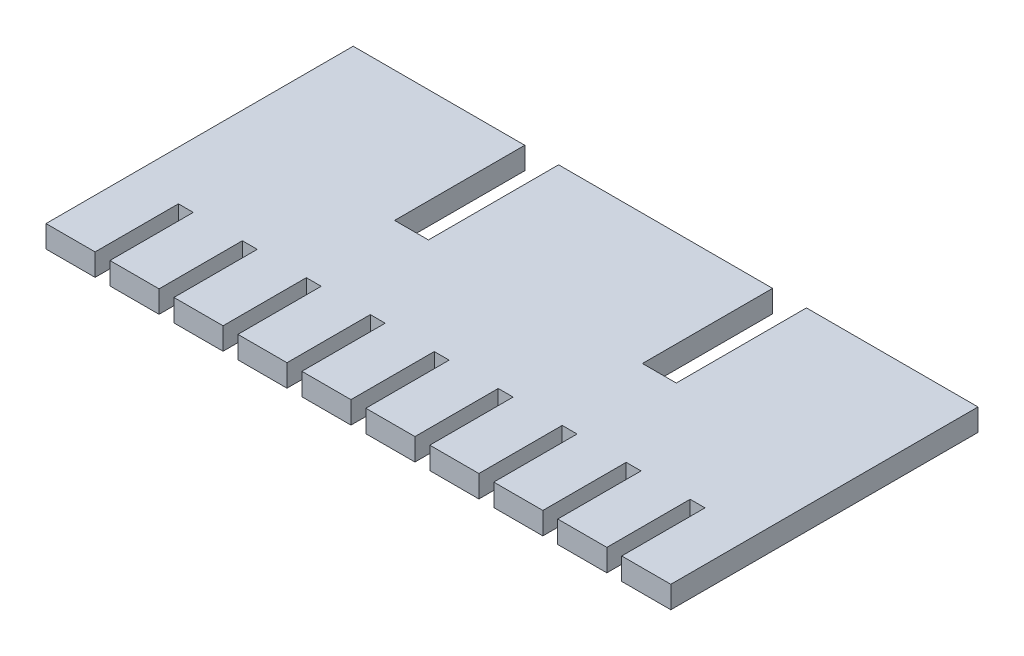
SolidWorks part; units mm, degrees
ref_plane "Front Plane" through (0, 0, 0) normal (0, 0, 1) x (1, 0, 0)
ref_plane "Top Plane" through (0, 0, 0) normal (0, 1, 0) x (1, 0, 0)
ref_plane "Right Plane" through (0, 0, 0) normal (1, 0, 0) x (0, 0, -1)
sketch "Sketch1" plane through (0, 0, 0) normal (0, 1, 0) x (1, 0, 0)
  line L0 (0, 0) -> (0, -29.5)
  line L1 (0, -29.5) -> (4.7139, -29.5)
  line L2 (4.7139, -29.5) -> (4.7139, -21.5)
  line L3 (4.7139, -21.5) -> (6.1429, -21.5)
  line L4 (6.1429, -21.5) -> (6.1429, -29.5)
  line L5 (6.1429, -29.5) -> (10.8568, -29.5)
  line L6 (10.8568, -29.5) -> (10.8568, -21.5)
  line L7 (10.8568, -21.5) -> (12.2858, -21.5)
  line L8 (12.2858, -21.5) -> (12.2858, -29.5)
  line L9 (12.2858, -29.5) -> (16.9997, -29.5)
  line L10 (16.9997, -29.5) -> (16.9997, -21.5)
  line L11 (16.9997, -21.5) -> (18.4287, -21.5)
  line L12 (18.4287, -21.5) -> (18.4287, -29.5)
  line L13 (18.4287, -29.5) -> (23.1426, -29.5)
  line L14 (23.1426, -29.5) -> (23.1426, -21.5)
  line L15 (23.1426, -21.5) -> (24.5716, -21.5)
  line L16 (24.5716, -21.5) -> (24.5716, -29.5)
  line L17 (24.5716, -29.5) -> (29.2855, -29.5)
  line L18 (29.2855, -29.5) -> (29.2855, -21.5)
  line L19 (29.2855, -21.5) -> (30.7145, -21.5)
  line L20 (30.7145, -21.5) -> (30.7145, -29.5)
  line L21 (30.7145, -29.5) -> (35.4284, -29.5)
  line L22 (35.4284, -29.5) -> (35.4284, -21.5)
  line L23 (35.4284, -21.5) -> (36.8574, -21.5)
  line L24 (36.8574, -21.5) -> (36.8574, -29.5)
  line L25 (36.8574, -29.5) -> (41.5713, -29.5)
  line L26 (41.5713, -29.5) -> (41.5713, -21.5)
  line L27 (41.5713, -21.5) -> (43.0003, -21.5)
  line L28 (43.0003, -21.5) -> (43.0003, -29.5)
  line L29 (43.0003, -29.5) -> (47.7142, -29.5)
  line L30 (47.7142, -29.5) -> (47.7142, -21.5)
  line L31 (47.7142, -21.5) -> (49.1432, -21.5)
  line L32 (49.1432, -21.5) -> (49.1432, -29.5)
  line L33 (49.1432, -29.5) -> (53.8571, -29.5)
  line L34 (53.8571, -29.5) -> (53.8571, -21.5)
  line L35 (53.8571, -21.5) -> (55.2861, -21.5)
  line L36 (55.2861, -21.5) -> (55.2861, -29.5)
  line L37 (55.2861, -29.5) -> (60, -29.5)
  line L38 (60, -29.5) -> (60, 0)
  line L39 (60, 0) -> (43.525, 0)
  line L48 (43.525, 0) -> (43.525, -12.5)
  line L49 (43.525, -12.5) -> (40.275, -12.5)
  line L50 (40.275, -12.5) -> (40.275, 0)
  line L51 (40.275, 0) -> (19.725, 0)
  line L52 (19.725, 0) -> (19.725, -12.5)
  line L53 (19.725, -12.5) -> (16.475, -12.5)
  line L54 (16.475, -12.5) -> (16.475, 0)
  line L55 (0, 0) -> (16.475, 0)
extrude "Boss-Extrude2" add sketch "Sketch1" along normal blind 2.121
